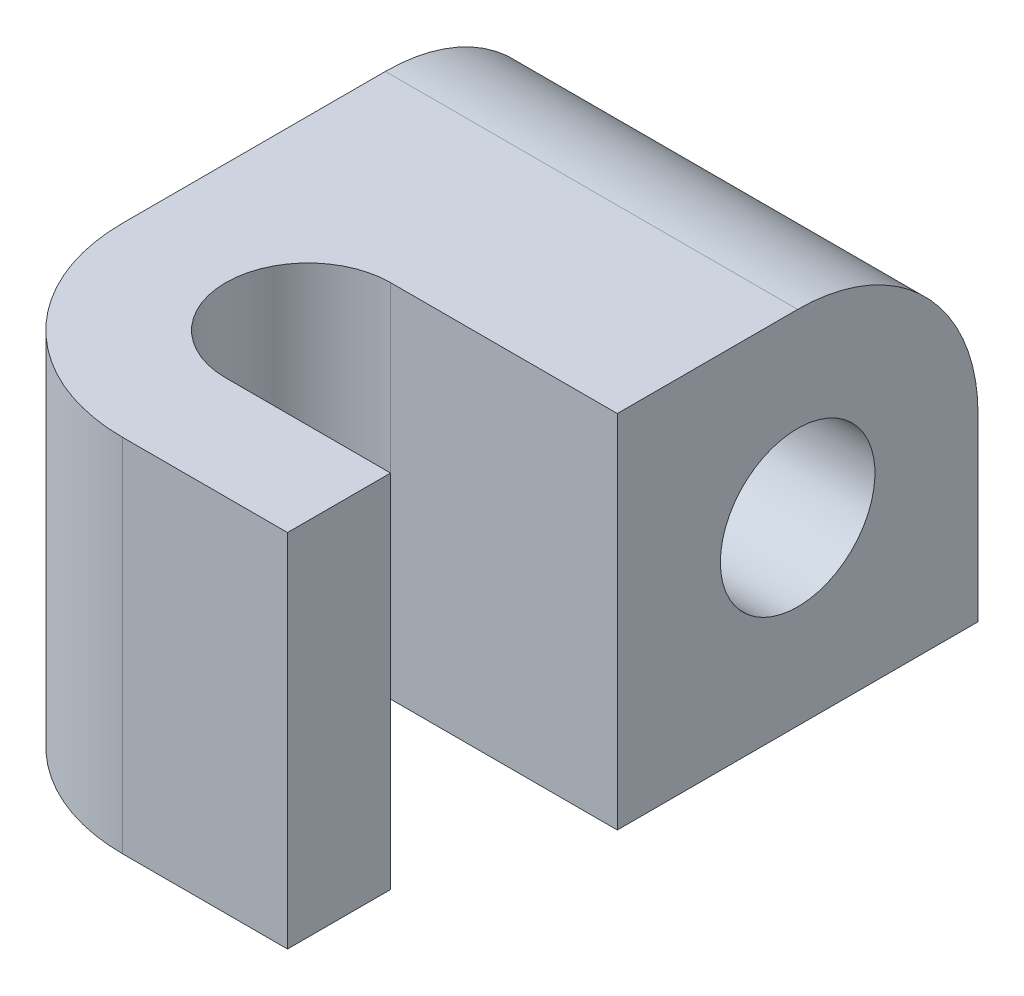
SolidWorks part; units mm, degrees
ref_plane "Front Plane" through (0, 0, 0) normal (0, 0, 1) x (1, 0, 0)
ref_plane "Top Plane" through (0, 0, 0) normal (0, 1, 0) x (1, 0, 0)
ref_plane "Right Plane" through (0, 0, 0) normal (1, 0, 0) x (0, 0, -1)
sketch "Sketch1" plane through (0, 0, 0) normal (1, 0, 0) x (0, 0, -1)
  line L0 (-8.75, 0) -> (8.75, 0)
  line L1 (8.75, 0) -> (8.75, 8.75)
  line L2 (-8.75, 8.75) -> (-8.75, 0)
  arc A0 (8.75, 8.75) -> (-8.75, 8.75) centre (0, 8.75) ccw
  circle A1 centre (0, 8.75) radius 3.75 construction
  dimension "D1" = 8.75
  dimension "D3" = 7.5
  dimension "D2" = 8.75
extrude "Boss-Extrude1" add sketch "Sketch1" along normal blind 20
sketch "Sketch2" plane through (0, 0, 0) normal (0, -1, 0) x (1, 0, 0)
  line L0 (0, 12.75) -> (0, 8.75)
  line L1 (9, 21.75) -> (17, 21.75)
  line L2 (17, 21.75) -> (17, 16.75)
  line L3 (17, 16.75) -> (9, 16.75)
  line L4 (0, 8.75) -> (9, 8.75) construction
  line L5 (20, 8.75) -> (0, 8.75) construction
  line L6 (9, 8.75) -> (20, 8.75)
  line L7 (20, 8.75) -> (20, 0)
  line L8 (20, 8.75) -> (20, -8.75) construction
  line L9 (20, 0) -> (0, 0)
  line L10 (0, 0) -> (0, 8.75)
  arc A0 (0, 12.75) -> (9, 21.75) centre (9, 12.75) cw
  arc A1 (9, 16.75) -> (9, 8.75) centre (9, 12.75) ccw
  dimension "D1" = 4
  dimension "D3" = 8
  dimension "D2" = 5
extrude "Boss-Extrude2" add sketch "Sketch2" against normal blind 17.5
sketch "Sketch3" plane through (0, 0, 0) normal (-1, 0, 0) x (0, 0, 1)
  circle A0 centre (0, 8.75) radius 3.75
  dimension "D1" = 7.5
extrude "Cut-Extrude1" cut sketch "Sketch3" against normal through all
